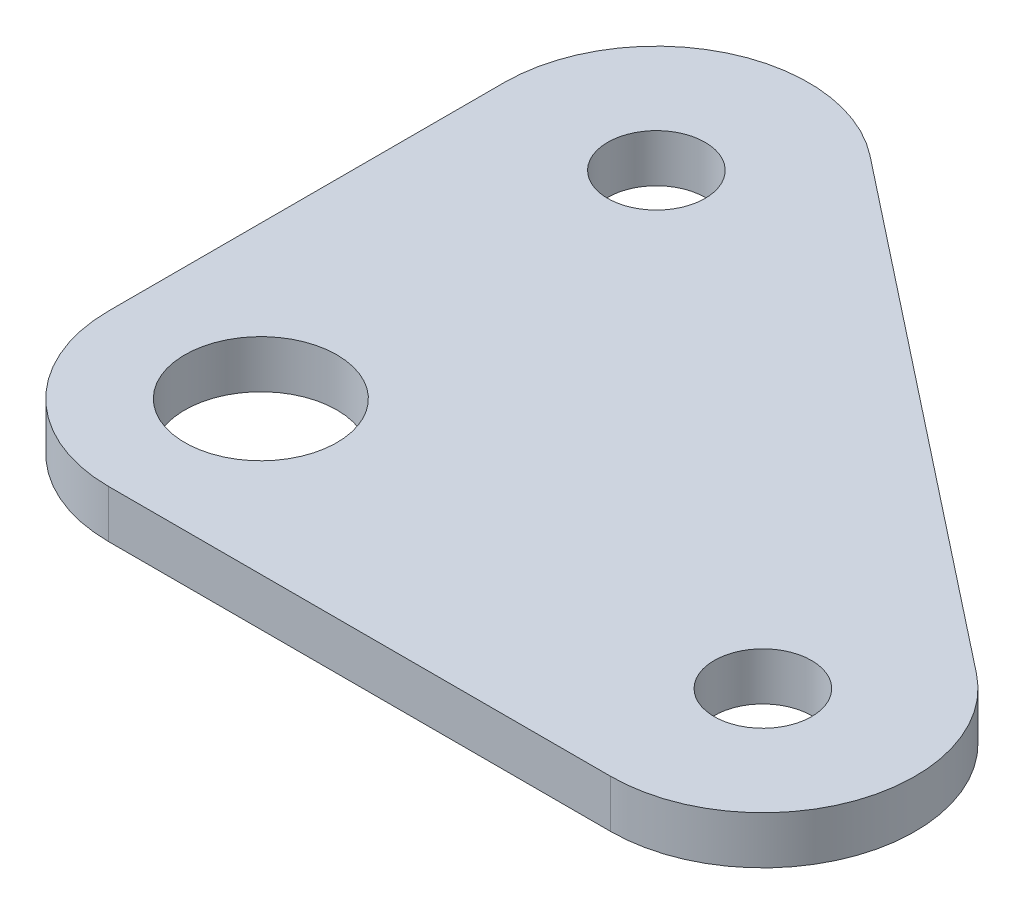
SolidWorks part; units mm, degrees
ref_plane "Front Plane" through (0, 0, 0) normal (0, 0, 1) x (1, 0, 0)
ref_plane "Top Plane" through (0, 0, 0) normal (0, 1, 0) x (1, 0, 0)
ref_plane "Right Plane" through (0, 0, 0) normal (1, 0, 0) x (0, 0, -1)
ref_plane "Plane1" through (0, 1.57, 0) normal (0, 1, 0) x (1, 0, 0)
sketch "Sketch1" plane through (0, 1.57, 0) normal (0, 1, 0) x (1, 0, 0)
  line L0 (0, -5) -> (16.5, -5)
  line L1 (19.5944, 3.9275) -> (3.0944, 16.9275)
  line L2 (-5, 13) -> (-5, 0)
  circle A0 centre (0, 13) radius 1.6
  circle A1 centre (16.5, 0) radius 1.6
  arc A2 (16.5, -5) -> (19.5944, 3.9275) centre (16.5, 0) ccw
  arc A3 (3.0944, 16.9275) -> (-5, 13) centre (0, 13) ccw
  arc A4 (-5, 0) -> (0, -5) centre (0, 0) ccw
  circle A5 centre (0, 0) radius 2.5
extrude "Boss-Extrude1" add sketch "Sketch1" against normal blind 1.57
